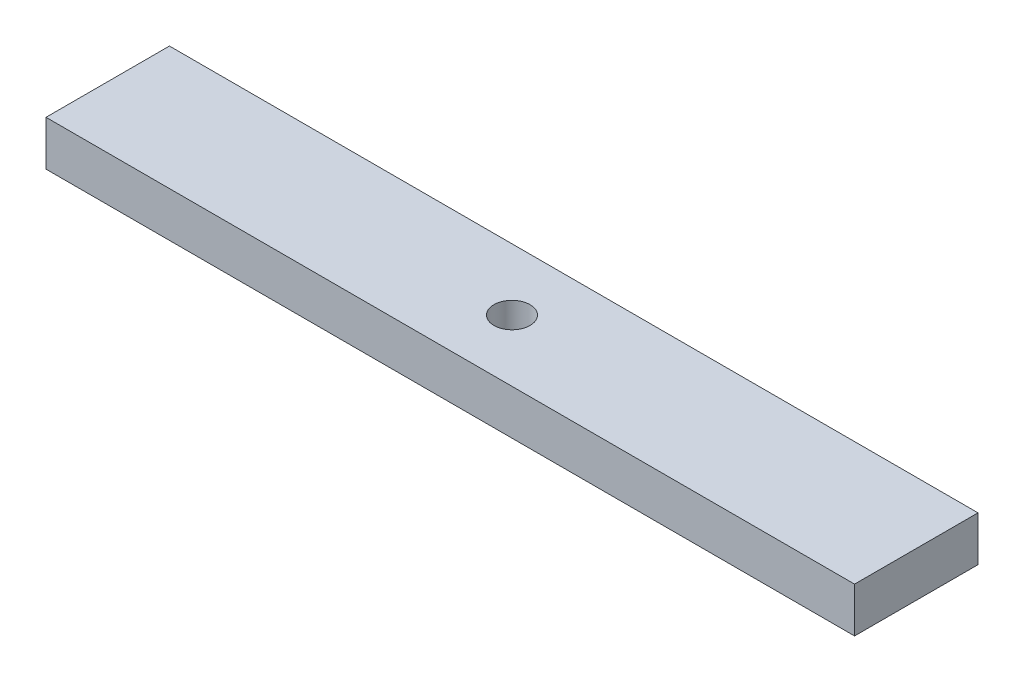
SolidWorks part; units mm, degrees
ref_plane "Front Plane" through (0, 0, 0) normal (0, 0, 1) x (1, 0, 0)
ref_plane "Top Plane" through (0, 0, 0) normal (0, 1, 0) x (1, 0, 0)
ref_plane "Right Plane" through (0, 0, 0) normal (1, 0, 0) x (0, 0, -1)
sketch "Sketch1" plane through (0, 0, 0) normal (0, 1, 0) x (1, 0, 0)
  line L0 (57.15, 0) -> (-57.15, 0) construction
  line L1 (-57.15, -8.7249) -> (57.15, -8.7249)
  line L2 (-57.15, -8.7249) -> (-57.15, 8.7249)
  line L3 (-57.15, 8.7249) -> (57.15, 8.7249)
  line L4 (57.15, -8.7249) -> (57.15, 8.7249)
  line L5 (-57.15, -8.7249) -> (57.15, 8.7249) construction
  line L6 (-57.15, 8.7249) -> (57.15, -8.7249) construction
  line L7 (53.975, -8.7249) -> (53.975, 8.7249) construction
  line L8 (-53.975, -8.7249) -> (-53.975, 8.7249) construction
  circle A0 centre (0, 0) radius 2.5527
  point P0 (0, 0)
  dimension "D1" = 17.4498
  dimension "D2" = 114.3
  dimension "D3" = 3.175
  dimension "D4" = 3.175
extrude "Boss-Extrude1" add sketch "Sketch1" along normal blind 6.35
